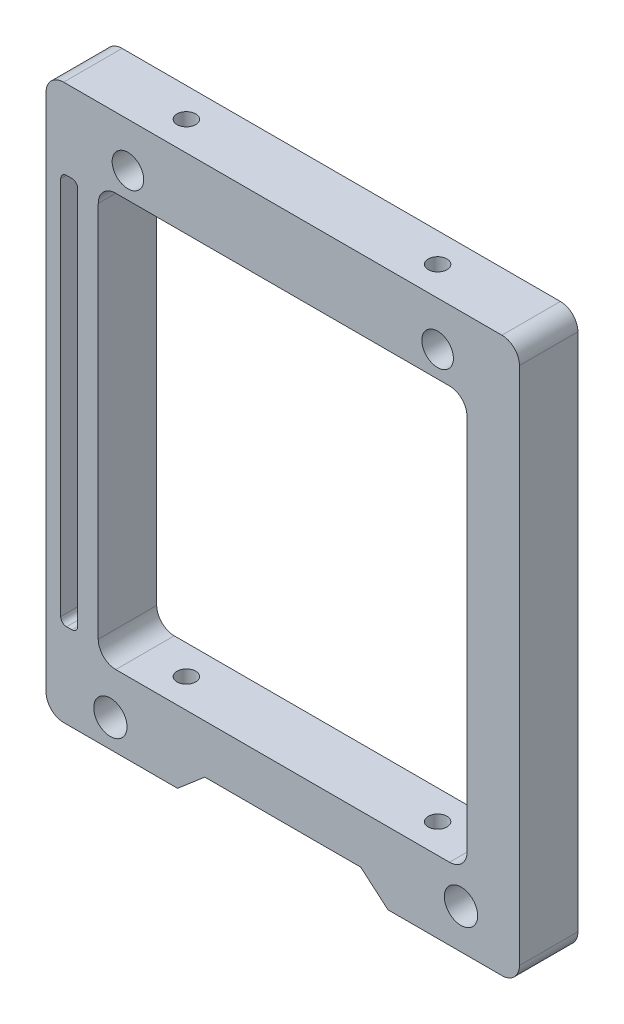
SolidWorks part; units mm, degrees
ref_plane "Спереди" through (0, 0, 0) normal (0, 0, 1) x (1, 0, 0)
ref_plane "Сверху" through (0, 0, 0) normal (0, 1, 0) x (1, 0, 0)
ref_plane "Справа" through (0, 0, 0) normal (1, 0, 0) x (0, 0, -1)
sketch "Эскиз2" plane through (0, 0, 0) normal (0, 0, 1) x (1, 0, 0)
  line L0 (0, 100.0976) -> (80.9803, 100.0976)
  line L1 (80.9803, 100.0976) -> (80.9803, 88.0976)
  line L2 (8.9232, 88.0976) -> (8.9232, 17.5329)
  line L3 (80.9803, 88.0976) -> (0, 88.0976)
  line L4 (14, 17.5329) -> (5, 17.5329)
  line L5 (0, 88.0976) -> (0, 100.0976)
  line L6 (80.9803, 17.5329) -> (0, 17.5329)
  line L7 (0, 17.5329) -> (0, 5.2193)
  line L8 (0, 5.2193) -> (22.4901, 5.2193)
  line L9 (80.9803, 5.2193) -> (80.9803, 17.5329)
  line L10 (0, 88.0976) -> (5, 88.0976)
  line L11 (5, 88.0976) -> (5, 17.5329)
  line L12 (5, 17.5329) -> (0, 17.5329)
  line L13 (0, 17.5329) -> (0, 88.0976)
  line L14 (80.9803, 88.0976) -> (80.9803, 17.5329)
  line L15 (80.9803, 17.5329) -> (75.9803, 17.5329)
  line L16 (75.9803, 17.5329) -> (75.9803, 88.0976)
  line L17 (75.9803, 88.0976) -> (80.9803, 88.0976)
  line L18 (5, 88.0976) -> (14, 88.0976)
  line L19 (72.0093, 88.0976) -> (72.0093, 17.5329)
  line L20 (66.9803, 17.5329) -> (75.9803, 17.5329)
  line L21 (75.9803, 17.5329) -> (75.9803, 88.0976)
  line L22 (75.9803, 88.0976) -> (66.9803, 88.0976)
  line L24 (22.4901, 5.2193) -> (27.1532, 9.2094)
  line L25 (27.1532, 9.2094) -> (53.8271, 9.2094)
  line L26 (58.4901, 5.2193) -> (80.9803, 5.2193)
  line L27 (58.4901, 5.2193) -> (53.8271, 9.2094)
  circle A0 centre (14, 92.5) radius 2.7
  circle A1 centre (66.9803, 92.5) radius 2.7
  circle A2 centre (11, 10) radius 2.85
  circle A3 centre (70.9803, 12) radius 2.85
extrude "Бобышка-Вытянуть1" add sketch "Эскиз2" along normal blind 10 contours L5 L3 L1 L0 A1 A0 | L13 L6 L11 L3 | L16 L6 L14 L3 | L8 L9 L6 L7 A3 A2 | L3 L19 L6 L16 | L3 L11 L4 L2
sketch "Эскиз6" plane through (0, 100.0976, 0) normal (0, 1, 0) x (1, 0, 0)
  line L0 (0, -10) -> (19, -10)
  line L1 (0, -10) -> (80.9803, -10) construction
  line L5 (0, -10) -> (80.9803, -10)
  line L6 (80.9803, -10) -> (40.4901, -10)
  circle A0 centre (19, -5) radius 1.6
  circle A1 centre (61.9803, -5) radius 1.6
extrude "Вырез-Вытянуть1" cut sketch "Эскиз6" against normal through all contours A0 | A1
sketch "Эскиз7" plane through (0, 0, 10) normal (0, 0, 1) x (1, 0, 0)
  line L1 (3.5014, 86.5318) -> (4.4138, 86.5318)
  line L2 (2.5014, 85.5318) -> (2.5014, 20.6715)
  line L3 (3.5014, 19.6715) -> (4.4138, 19.6715)
  line L4 (5.4138, 85.5318) -> (5.4138, 20.6715)
  arc A0 (3.5014, 19.6715) -> (2.5014, 20.6715) centre (3.5014, 20.6715) cw
  arc A1 (4.4138, 19.6715) -> (5.4138, 20.6715) centre (4.4138, 20.6715) ccw
  arc A2 (5.4138, 85.5318) -> (4.4138, 86.5318) centre (4.4138, 85.5318) ccw
  arc A3 (3.5014, 86.5318) -> (2.5014, 85.5318) centre (3.5014, 85.5318) ccw
  dimension "D1" = 1
extrude "Вырез-Вытянуть2" cut sketch "Эскиз7" against normal blind 10
fillet "Скругление1" radius 3 1 edges at (72.0093, 88.0976, 5)
fillet "Скругление2" radius 3 1 edges at (8.9232, 88.0976, 5)
fillet "Скругление3" radius 3 1 edges at (8.9232, 17.5329, 5)
fillet "Скругление4" radius 3 1 edges at (72.0093, 17.5329, 5)
fillet "Скругление5" radius 3 2 edges at (0, 100.0976, 5) (80.9803, 100.0976, 5)
fillet "Скругление6" radius 3 2 edges at (0, 5.2193, 5) (80.9803, 5.2193, 5)
sketch "Эскиз8" plane through (0, 100.0976, 0) normal (0, 1, 0) x (1, 0, 0)
  line L0 (0, 0) -> (0, -10)
  line L1 (0, -10) -> (80.9803, -10)
  line L2 (80.9803, -10) -> (80.9803, 0)
  line L3 (80.9803, 0) -> (0, 0)
  line L4 (0, 0) -> (9, 0)
  line L5 (9, 0) -> (8.9232, -10)
  line L6 (40.4901, -10) -> (40.4901, 0)
  line L7 (71.9803, 0) -> (72.0571, -10)
  circle A0 centre (19, -5) radius 1.6
  circle A1 centre (61.9803, -5) radius 1.6
